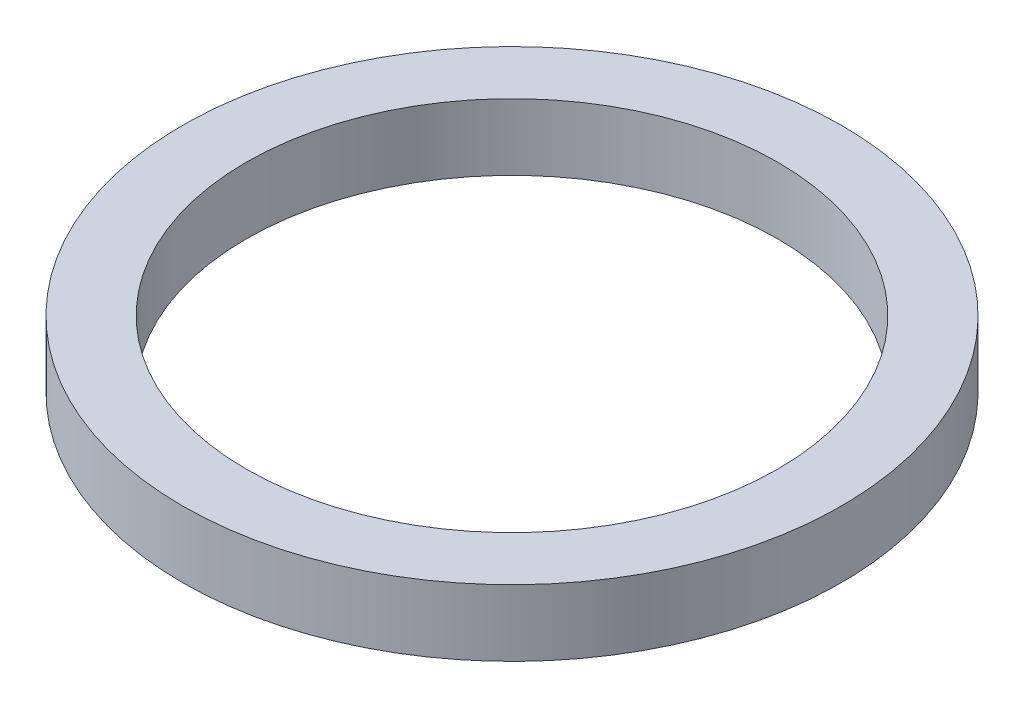
SolidWorks part; units mm, degrees
ref_plane "Front Plane" through (0, 0, 0) normal (0, 0, 1) x (1, 0, 0)
ref_plane "Top Plane" through (0, 0, 0) normal (0, 1, 0) x (1, 0, 0)
ref_plane "Right Plane" through (0, 0, 0) normal (1, 0, 0) x (0, 0, -1)
sketch "Sketch1" plane through (0, 0, 0) normal (0, 1, 0) x (1, 0, 0)
  circle A0 centre (0, 0) radius 6.35
  circle A1 centre (0, 0) radius 7.874
  dimension "D1" = 12.7
  dimension "D2" = 15.748
extrude "Boss-Extrude1" add sketch "Sketch1" along normal blind 1.5875
